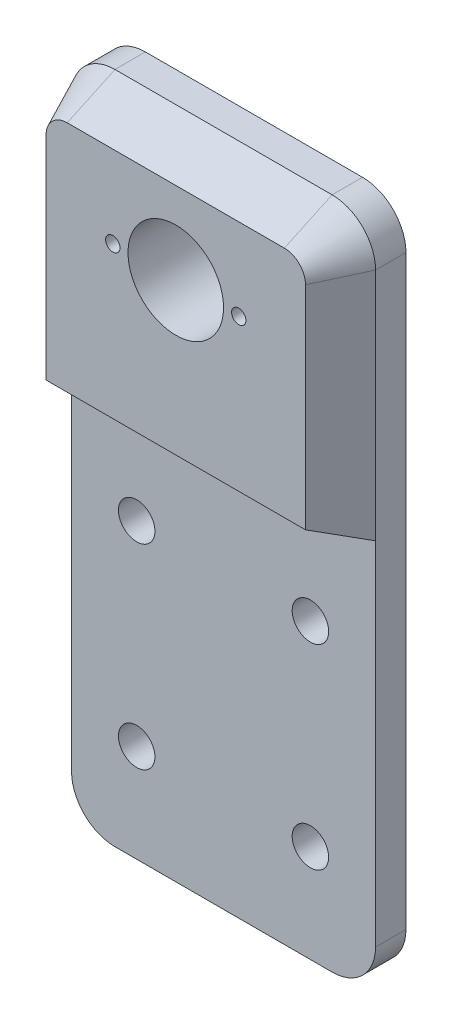
SolidWorks part; units mm, degrees
ref_plane "Front Plane" through (0, 0, 0) normal (0, 0, 1) x (1, 0, 0)
ref_plane "Top Plane" through (0, 0, 0) normal (0, 1, 0) x (1, 0, 0)
ref_plane "Right Plane" through (0, 0, 0) normal (1, 0, 0) x (0, 0, -1)
sketch "Sketch1" plane through (0, 0, 0) normal (0, 0, 1) x (1, 0, 0)
  line L0 (-35, -52.5) -> (35, -52.5) construction
  line L1 (-25, 80) -> (25, 80)
  line L2 (-35, 70) -> (-35, -65)
  line L3 (-25, -75) -> (25, -75)
  line L4 (35, 70) -> (35, -65)
  line L5 (-35, -7.5) -> (35, -7.5) construction
  line L6 (-35, 15) -> (35, 15) construction
  line L7 (-35, 56) -> (35, 56) construction
  line L8 (0, 80) -> (0, -75) construction
  line L9 (-20, -7.5) -> (-20, -52.5) construction
  line L10 (20, -7.5) -> (20, -52.5) construction
  arc A0 (-35, 70) -> (-25, 80) centre (-25, 70) cw
  arc A1 (35, 70) -> (25, 80) centre (25, 70) ccw
  arc A2 (35, -65) -> (25, -75) centre (25, -65) cw
  arc A3 (-25, -75) -> (-35, -65) centre (-25, -65) cw
  circle A5 centre (-20, -7.5) radius 4.2
  circle A6 centre (20, -7.5) radius 4.2
  circle A7 centre (20, -52.5) radius 4.2
  circle A8 centre (-20, -52.5) radius 4.2
  point P0 (0, 0)
  point P8 (-35, 80)
  point P13 (35, -75)
  point P16 (-35, -75)
  dimension "D3" = 10
  dimension "D8" = 15
  dimension "D1" = 155
  dimension "D2" = 70
  dimension "D4" = 22.5
  dimension "D5" = 45
  dimension "D6" = 22.5
  dimension "D7" = 41
  dimension "D9" = 15
extrude "Boss-Extrude1" add sketch "Sketch1" against normal blind 7
sketch "Sketch3" plane through (0, 0, 0) normal (0, 0, 1) x (1, 0, 0)
  line L0 (-35, 16) -> (35, 16)
  line L1 (-35, 70) -> (-35, -65) construction
  line L2 (35, -65) -> (35, 70) construction
  line L3 (-25, -75) -> (25, -75) construction
  line L4 (-35, 16) -> (-35, 70)
  line L5 (-25, 80) -> (25, 80)
  line L6 (35, 70) -> (35, 16)
  arc A0 (-35, 70) -> (-25, 80) centre (-25, 70) cw
  arc A1 (25, 80) -> (35, 70) centre (25, 70) cw
  dimension "D2" = 10
  dimension "D1" = 91
extrude "Boss-Extrude2" add sketch "Sketch3" along normal blind 11 draft 25
sketch "Sketch5" plane through (0, 0, 11) normal (0, 0, 1) x (1, 0, 0)
  line L0 (0, 56) -> (-14.5, 56) construction
  line L1 (0, 56) -> (14.5, 56) construction
  circle A0 centre (-14.5, 56) radius 1.65
  circle A1 centre (14.5, 56) radius 1.65
  circle A2 centre (0, 56) radius 11
  dimension "D1" = 14.5
  dimension "D2" = 14.5
extrude "Cut-Extrude1" cut sketch "Sketch5" against normal through all
